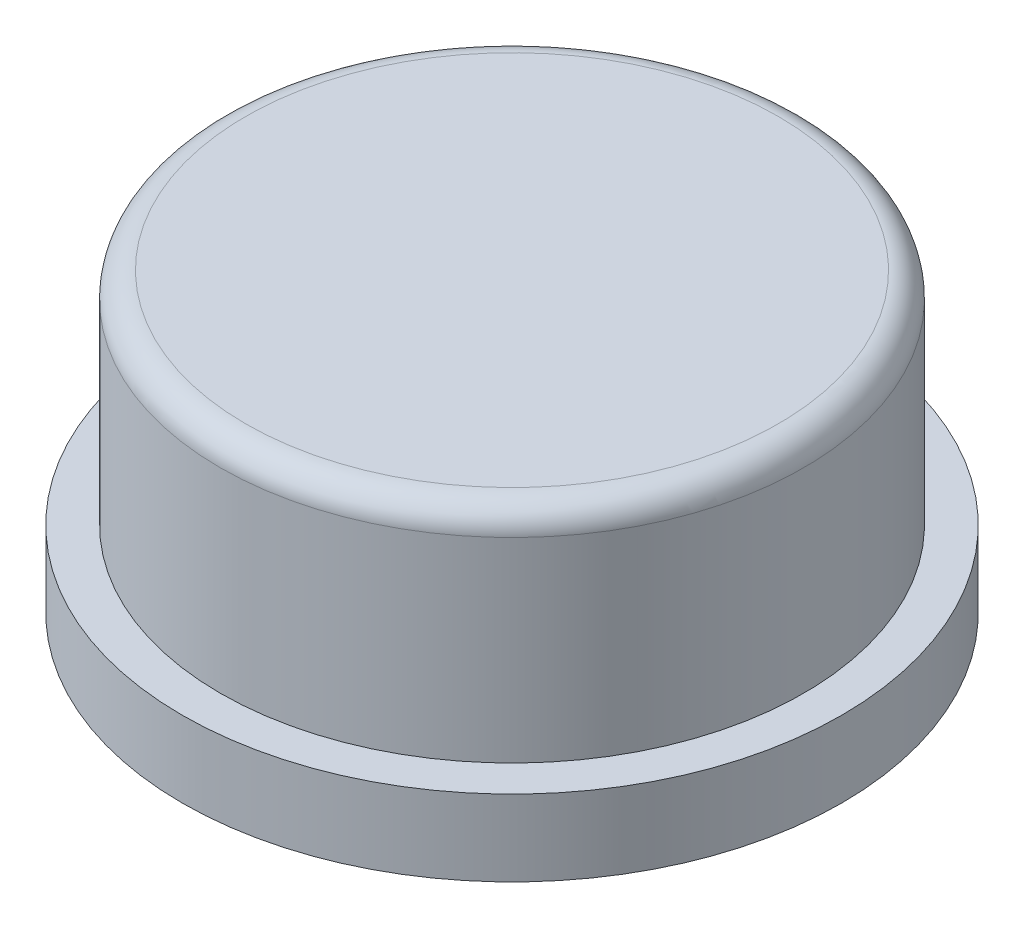
SolidWorks part; units mm, degrees
ref_plane "Front Plane" through (0, 0, 0) normal (0, 0, 1) x (1, 0, 0)
ref_plane "Top Plane" through (0, 0, 0) normal (0, 1, 0) x (1, 0, 0)
ref_plane "Right Plane" through (0, 0, 0) normal (1, 0, 0) x (0, 0, -1)
sketch "Sketch1" plane through (0, 0, 0) normal (0, 1, 0) x (1, 0, 0)
  circle A0 centre (0, 0) radius 6.5
  circle A1 centre (0, 0) radius 5
  dimension "D1" = 13
  dimension "D2" = 10
extrude "Boss-Extrude1" add sketch "Sketch1" along normal blind 1.5
sketch "Sketch2" plane through (0, 1.5, 0) normal (0, 1, 0) x (1, 0, 0)
  circle A0 centre (0, 0) radius 5.75
  circle A1 centre (0, 0) radius 5
  dimension "D1" = 11.5
  dimension "D2" = 10
extrude "Boss-Extrude2" add sketch "Sketch2" along normal blind 4.35
fillet "Fillet1" radius 0.5 1 edges at (0, 5.85, 5.75)
sketch "Sketch3" plane through (0, 5.85, 0) normal (0, 1, 0) x (1, 0, 0)
  circle A0 centre (0, 0) radius 5
  circle A1 centre (0, 0) radius 5 construction
extrude "Boss-Extrude3" add sketch "Sketch3" against normal blind 4
